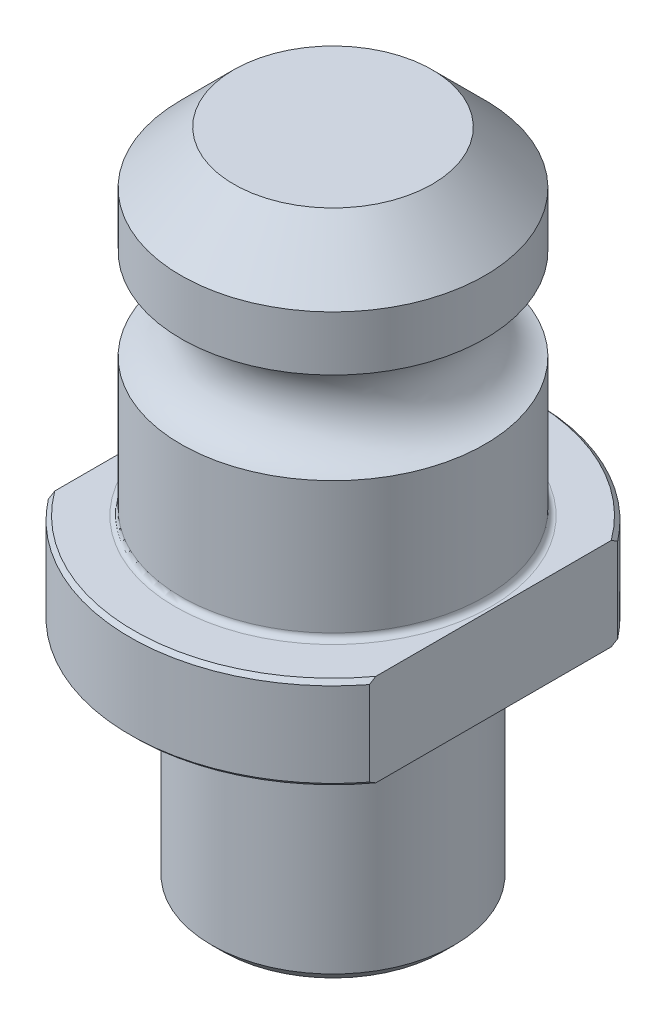
SolidWorks part; units mm, degrees
ref_plane "Front Plane" through (0, 0, 0) normal (0, 0, 1) x (1, 0, 0)
ref_plane "Top Plane" through (0, 0, 0) normal (0, 1, 0) x (1, 0, 0)
ref_plane "Right Plane" through (0, 0, 0) normal (1, 0, 0) x (0, 0, -1)
sketch "Sketch1" plane through (0, 0, 0) normal (0, 0, 1) x (1, 0, 0)
  line L0 (0, 55.9816) -> (0, -30.0736)
  line L1 (0, -30.0736) -> (-15.875, -30.0736)
  line L2 (-15.875, -30.0736) -> (-15.875, -4.318)
  line L3 (-15.875, -4.318) -> (-13.6017, -4.318)
  line L4 (-13.6017, -4.318) -> (-13.6017, -1.27)
  line L5 (-14.8717, 0) -> (-26.4922, 0)
  line L6 (-26.4922, 0) -> (-26.4922, 12.0396)
  line L7 (-26.4922, 12.0396) -> (-19.8374, 12.0396)
  line L8 (-19.8374, 12.0396) -> (-19.8374, 30.0228)
  line L9 (-19.8374, 49.0982) -> (-12.954, 55.9816)
  line L10 (-12.954, 55.9816) -> (0, 55.9816)
  line L11 (0, -30.0736) -> (0, -73.6863) construction
  line L12 (-19.8374, 41.9608) -> (-19.8374, 49.0982)
  arc A0 (-19.8374, 30.0228) -> (-19.8374, 41.9608) centre (-20.9266, 35.9918) ccw
  arc A1 (-14.8717, 0) -> (-13.6017, -1.27) centre (-14.8717, -1.27) cw
  dimension "D13" = 29.718
  dimension "D14" = 1.27
  dimension "D15" = 6.0676
  dimension "D1" = 31.75
  dimension "D2" = 27.2034
  dimension "D3" = 52.9844
  dimension "D4" = 39.6748
  dimension "D5" = 30.0736
  dimension "D6" = 12.0396
  dimension "D7" = 4.318
  dimension "D8" = 45
  dimension "D9" = 25.908
  dimension "D10" = 43.942
  dimension "D11" = 17.9832
  dimension "D12" = 11.938
revolve "Revolve1" add sketch "Sketch1" angle 360 about L11
chamfer "Chamfer1" distance 0.508 angle 45 2 edges at (-26.4922, 0, 0) (-26.4922, 12.0396, 0)
chamfer "Chamfer2" distance 1.524 angle 45 1 edges at (-15.875, -30.0736, 0)
sketch "Sketch2" plane through (0, 12.0396, 0) normal (0, 1, 0) x (1, 0, 0)
  line L0 (-20.955, 16.2088) -> (-20.955, -16.2088)
  line L1 (20.955, 16.2088) -> (20.955, -16.2088)
  circle A0 centre (0, 0) radius 26.4922 construction
  arc A1 (20.955, -16.2088) -> (20.955, 16.2088) centre (0, 0) ccw
  arc A2 (-20.955, 16.2088) -> (-20.955, -16.2088) centre (0, 0) ccw
  dimension "D1" = 20.955
  dimension "D2" = 20.955
extrude "Cut-Extrude1" cut sketch "Sketch2" against normal through all
fillet "Fillet1" radius 0.762 1 edges at (-19.8374, 12.0396, 0)
